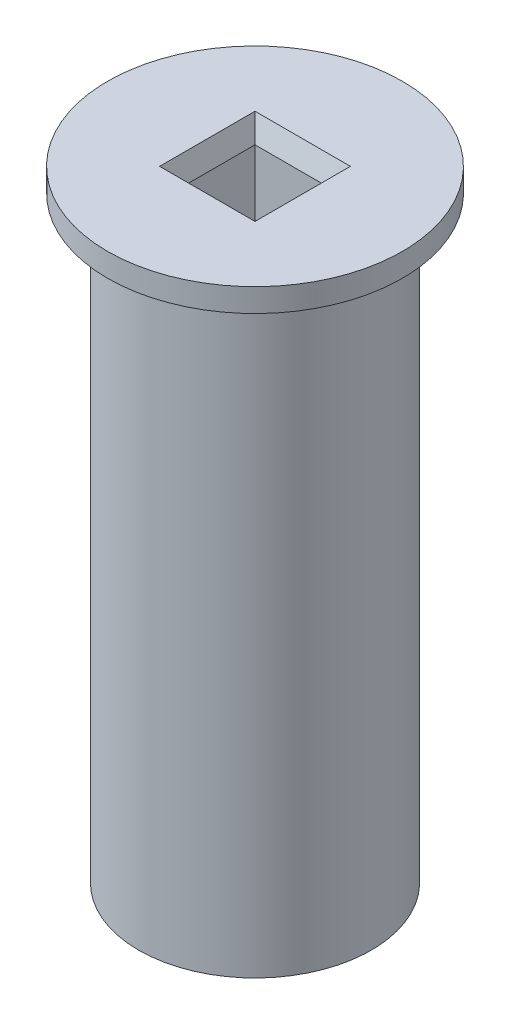
SolidWorks part; units mm, degrees
ref_plane "Спереди" through (0, 0, 0) normal (0, 0, 1) x (1, 0, 0)
ref_plane "Сверху" through (0, 0, 0) normal (0, 1, 0) x (1, 0, 0)
ref_plane "Справа" through (0, 0, 0) normal (1, 0, 0) x (0, 0, -1)
sketch "Эскиз1" plane through (0, 0, 0) normal (0, 1, 0) x (1, 0, 0)
  line L1 (5.15, -5.15) -> (-5.15, -5.15)
  line L2 (5.15, -5.15) -> (5.15, 5.15)
  line L3 (5.15, 5.15) -> (-5.15, 5.15)
  line L4 (-5.15, -5.15) -> (-5.15, 5.15)
  line L5 (5.15, -5.15) -> (-5.15, 5.15) construction
  line L6 (5.15, 5.15) -> (-5.15, -5.15) construction
  circle A0 centre (0, 0) radius 15
  dimension "D1" = 30
  dimension "D2" = 10.3
extrude "Бобышка-Вытянуть1" add sketch "Эскиз1" along normal blind 80
sketch "Sketch1" plane through (0, 80, 0) normal (0, 1, 0) x (1, 0, 0)
  line L1 (5.15, -5.15) -> (-5.15, -5.15)
  line L2 (5.15, -5.15) -> (5.15, 5.15)
  line L3 (5.15, 5.15) -> (-5.15, 5.15)
  line L4 (-5.15, -5.15) -> (-5.15, 5.15)
  line L5 (5.15, -5.15) -> (-5.15, 5.15) construction
  line L6 (5.15, 5.15) -> (-5.15, -5.15) construction
  circle A0 centre (0, 0) radius 19
  dimension "D1" = 38
extrude "Boss-Extrude1" add sketch "Sketch1" against normal blind 3
chamfer "Chamfer1" distance 1 angle 70 4 edges at (5.15, 80, 0) (0, 80, 5.15) (-5.15, 80, 0) (0, 80, -5.15)
